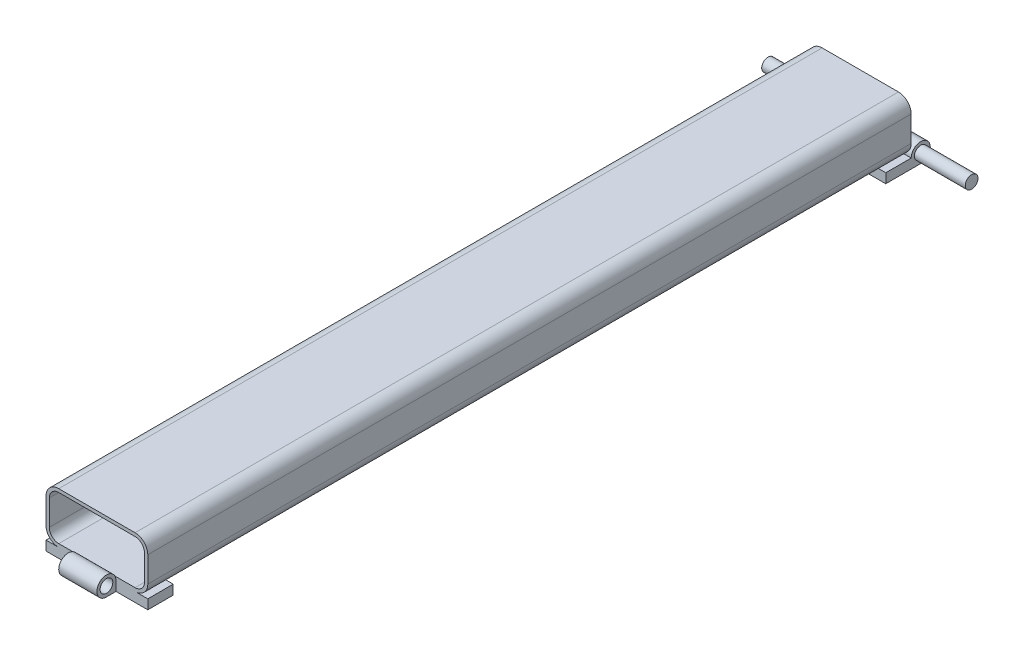
SolidWorks part; units mm, degrees
ref_plane "Front Plane" through (0, 0, 0) normal (0, 0, 1) x (1, 0, 0)
ref_plane "Top Plane" through (0, 0, 0) normal (0, 1, 0) x (1, 0, 0)
ref_plane "Right Plane" through (0, 0, 0) normal (1, 0, 0) x (0, 0, -1)
sketch "Sketch1" plane through (0, 0, 0) normal (0, 0, 1) x (1, 0, 0)
  line L0 (-19.05, 11.049) -> (19.05, 11.049)
  line L1 (-19.05, -12.7) -> (19.05, -12.7)
  line L2 (-25.4, -6.35) -> (-25.4, 6.35)
  line L3 (-19.05, 12.7) -> (19.05, 12.7)
  line L4 (25.4, -6.35) -> (25.4, 6.35)
  line L5 (-25.4, -12.7) -> (25.4, 12.7) construction
  line L6 (-25.4, 12.7) -> (25.4, -12.7) construction
  line L7 (23.749, -6.35) -> (23.749, 6.35)
  line L8 (-19.05, -11.049) -> (19.05, -11.049)
  line L9 (-23.749, -6.35) -> (-23.749, 6.35)
  arc A0 (-19.05, -12.7) -> (-25.4, -6.35) centre (-19.05, -6.35) cw
  arc A1 (19.05, -12.7) -> (25.4, -6.35) centre (19.05, -6.35) ccw
  arc A2 (19.05, 12.7) -> (25.4, 6.35) centre (19.05, 6.35) cw
  arc A3 (-25.4, 6.35) -> (-19.05, 12.7) centre (-19.05, 6.35) cw
  arc A4 (-23.749, 6.35) -> (-19.05, 11.049) centre (-19.05, 6.35) cw
  arc A5 (19.05, 11.049) -> (23.749, 6.35) centre (19.05, 6.35) cw
  arc A6 (19.05, -11.049) -> (23.749, -6.35) centre (19.05, -6.35) ccw
  arc A7 (-19.05, -11.049) -> (-23.749, -6.35) centre (-19.05, -6.35) cw
  point P0 (0, 0)
  dimension "D3" = 6.35
  dimension "D1" = 50.8
  dimension "D2" = 25.4
  dimension "D4" = 1.651
extrude "Boss-Extrude1" add sketch "Sketch1" along normal mid plane 381
sketch "Sketch2" plane through (25.4, 0, 0) normal (1, 0, 0) x (0, 0, -1)
  line L0 (177.8, -12.7) -> (177.8, -17.4625)
  line L1 (-190.5, -12.7) -> (190.5, -12.7) construction
  line L2 (177.8, -17.4625) -> (195.2625, -17.4625)
  line L3 (190.5, -12.7) -> (190.5, -6.35) construction
  line L4 (190.5, -6.35) -> (190.5, 6.35) construction
  line L5 (190.5, -12.7) -> (177.8, -12.7)
  arc A0 (195.2625, -17.4625) -> (190.5, -12.7) centre (195.2625, -12.7) ccw
  dimension "D1" = 4.7625
  dimension "D2" = 4.7625
  dimension "D3" = 12.7
extrude "Boss-Extrude2" add sketch "Sketch2" against normal through all
mirror "Mirror1" about plane through (0, 0, 0) normal (0, 0, 1) of "Boss-Extrude2"
sketch "Sketch3" plane through (0, 0, 0) normal (1, 0, 0) x (0, 0, -1)
  circle A0 centre (195.2625, -12.7) radius 3.175
  dimension "D1" = 6.35
extrude "Boss-Extrude3" add sketch "Sketch3" along normal mid plane 101.6
sketch "Sketch4" plane through (0, -17.4625, 0) normal (0, -1, 0) x (1, 0, 0)
  line L0 (-25.4, 200.025) -> (-9.525, 200.025)
  line L1 (-9.525, 200.025) -> (-9.525, 190.5)
  line L2 (-9.525, 190.5) -> (-25.4, 190.5)
  line L3 (-25.4, 190.5) -> (-25.4, 200.025)
  line L4 (25.4, 200.025) -> (25.4, 190.5)
  line L5 (25.4, 177.8) -> (25.4, 195.2625) construction
  line L6 (25.4, 190.5) -> (9.525, 190.5)
  line L7 (9.525, 190.5) -> (9.525, 200.025)
  line L8 (25.4, 200.025) -> (-25.4, 200.025) construction
  line L9 (9.525, 200.025) -> (25.4, 200.025)
  line L10 (0, 200.025) -> (0, 177.8) construction
  line L11 (25.4, 200.025) -> (-25.4, 200.025) construction
  line L12 (-19.05, 177.8) -> (19.05, 177.8) construction
  dimension "D1" = 19.05
extrude "Cut-Extrude1" cut sketch "Sketch4" against normal through all
sketch "Sketch5" plane through (9.525, 0, 0) normal (1, 0, 0) x (0, 0, -1)
  circle A0 centre (-195.2625, -12.7) radius 3.175
  dimension "D1" = 6.35
extrude "Cut-Extrude2" cut sketch "Sketch5" against normal through all
